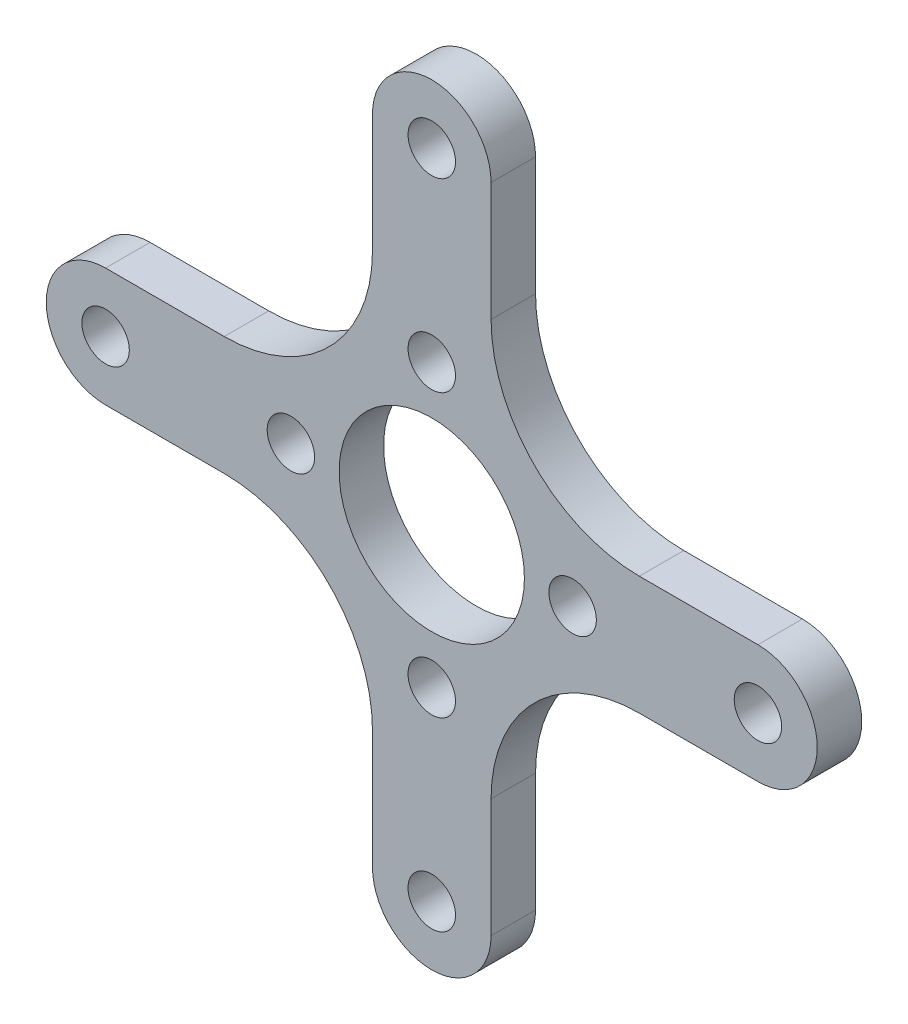
SolidWorks part; units mm, degrees
ref_plane "Front Plane" through (0, 0, 0) normal (0, 0, 1) x (1, 0, 0)
ref_plane "Top Plane" through (0, 0, 0) normal (0, 1, 0) x (1, 0, 0)
ref_plane "Right Plane" through (0, 0, 0) normal (1, 0, 0) x (0, 0, -1)
sketch "Эскиз1" plane through (0, 0, 0) normal (0, 0, 1) x (1, 0, 0)
  line L0 (-49.0565, 0) -> (61.1532, 0) construction
  line L1 (0, 58.6621) -> (0, -67.8855) construction
  line L2 (-22, 4) -> (-14, 4)
  line L3 (-4, 14) -> (-4, 22)
  line L4 (4, 14) -> (4, 22)
  line L5 (22, 4) -> (14, 4)
  line L6 (22, -4) -> (14, -4)
  line L7 (4, -14) -> (4, -22)
  line L8 (-4, -14) -> (-4, -22)
  line L9 (-22, -4) -> (-14, -4)
  circle A0 centre (0, 0) radius 6.25
  circle A1 centre (-9.5, 0) radius 1.6
  circle A2 centre (-22, 0) radius 1.6
  arc A3 (-22, -4) -> (-22, 4) centre (-22, 0) cw
  circle A4 centre (0, 9.5) radius 1.6
  circle A5 centre (0, 22) radius 1.6
  arc A6 (4, 22) -> (-4, 22) centre (0, 22) ccw
  arc A7 (-14, 4) -> (-4, 14) centre (-14, 14) ccw
  circle A8 centre (9.5, 0) radius 1.6
  arc A9 (14, 4) -> (4, 14) centre (14, 14) cw
  arc A10 (22, -4) -> (22, 4) centre (22, 0) ccw
  circle A11 centre (22, 0) radius 1.6
  arc A12 (14, -4) -> (4, -14) centre (14, -14) ccw
  arc A13 (-14, -4) -> (-4, -14) centre (-14, -14) cw
  arc A14 (4, -22) -> (-4, -22) centre (0, -22) cw
  circle A15 centre (0, -22) radius 1.6
  circle A16 centre (0, -9.5) radius 1.6
  point P22 (0, 0)
  point P23 (0, 0)
  point P24 (0, 0)
  point P25 (0, 0)
  point P26 (0, 0)
  dimension "D1" = 12.5
  dimension "D2" = 9.5
  dimension "D3" = 3.2
  dimension "D4" = 3.2
  dimension "D6" = 4
  dimension "D7" = 22
  dimension "D8" = 4
  dimension "D9" = 10
  dimension "D10" = 52
  dimension "D5" = 22
  dimension "9.5" = 9.5
extrude "Бобышка-Вытянуть1" add sketch "Эскиз1" along normal mid plane 3
